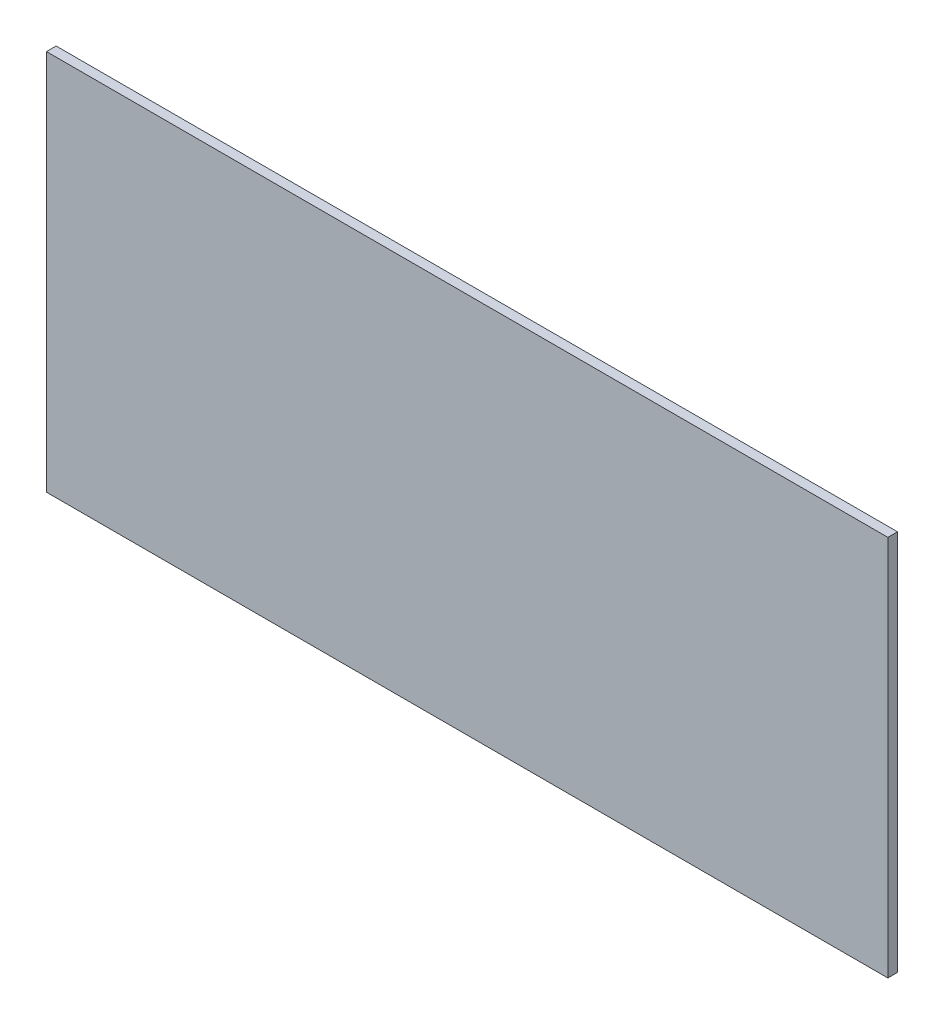
SolidWorks part; units mm, degrees
ref_plane "Front Plane" through (0, 0, 0) normal (0, 0, 1) x (1, 0, 0)
ref_plane "Top Plane" through (0, 0, 0) normal (0, 1, 0) x (1, 0, 0)
ref_plane "Right Plane" through (0, 0, 0) normal (1, 0, 0) x (0, 0, -1)
sketch "Sketch1" plane through (0, 0, 0) normal (0, 0, 1) x (1, 0, 0)
  line L0 (-130.64, 59.25) -> (130.64, 59.25)
  line L1 (-130.64, 59.25) -> (-130.64, -59.25)
  line L2 (-130.64, -59.25) -> (130.64, -59.25)
  line L3 (130.64, -59.25) -> (130.64, 59.25)
  point P2 (0, 59.25)
  point P3 (130.64, 0)
  dimension "D1" = 261.28
  dimension "D2" = 118.5
extrude "Boss-Extrude1" add sketch "Sketch1" along normal blind 3
